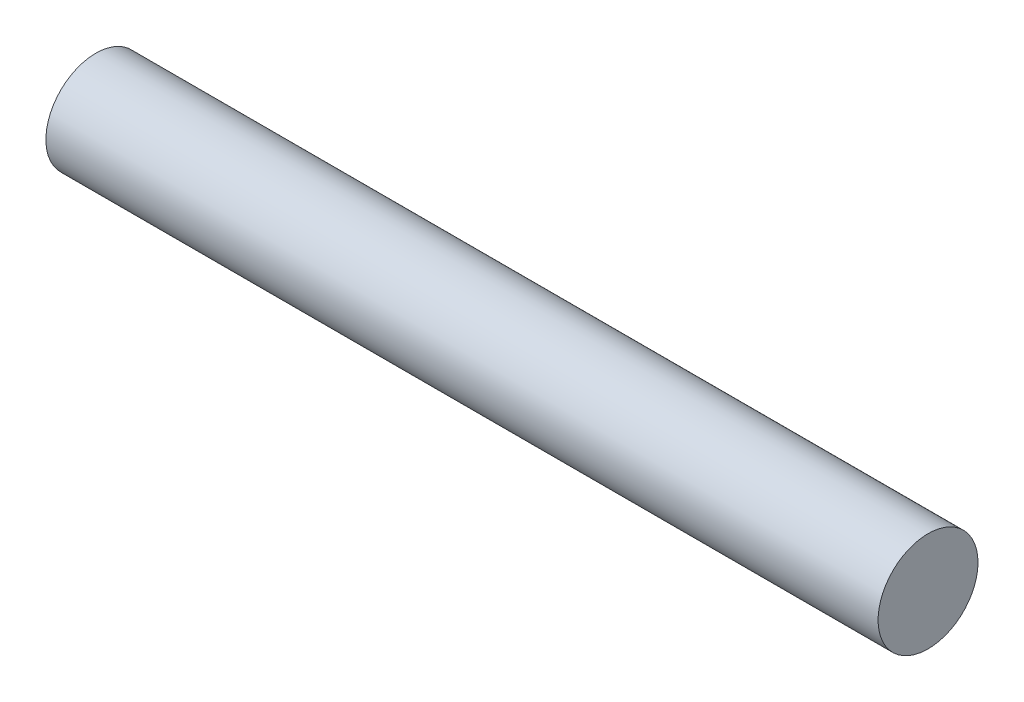
SolidWorks part; units mm, degrees
ref_plane "Front Plane" through (0, 0, 0) normal (0, 0, 1) x (1, 0, 0)
ref_plane "Top Plane" through (0, 0, 0) normal (0, 1, 0) x (1, 0, 0)
ref_plane "Right Plane" through (0, 0, 0) normal (1, 0, 0) x (0, 0, -1)
sketch "Sketch1" plane through (0, 0, 0) normal (1, 0, 0) x (0, 0, -1)
  circle A0 centre (0, 0) radius 2.3813
  dimension "D1" = 4.7625
extrude "Boss-Extrude1" add sketch "Sketch1" along normal blind 39.6748
